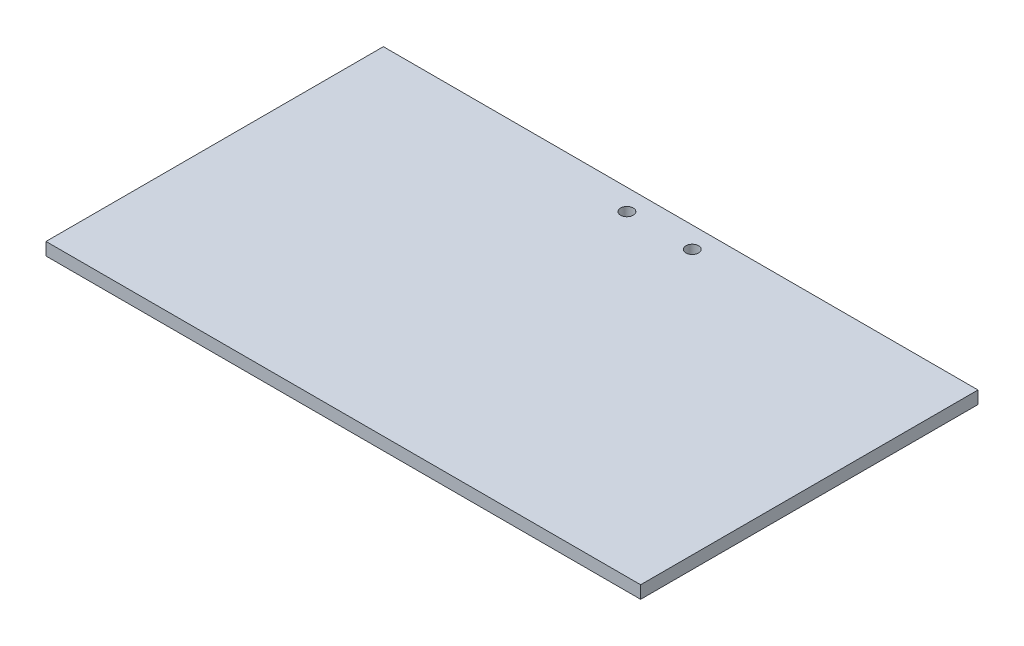
SolidWorks part; units mm, degrees
material "ｱｸﾘﾙ (中-上級の耐衝撃性)"
ref_plane "正面" through (0, 0, 0) normal (0, 0, 1) x (1, 0, 0)
ref_plane "平面" through (0, 0, 0) normal (0, 1, 0) x (1, 0, 0)
ref_plane "右側面" through (0, 0, 0) normal (1, 0, 0) x (0, 0, -1)
sketch "ｽｹｯﾁ1" plane through (0, 0, 0) normal (0, 1, 0) x (1, 0, 0)
  line L1 (0, 0) -> (-141, 0)
  line L2 (0, 0) -> (0, 80)
  line L3 (0, 80) -> (-141, 80)
  line L4 (-141, 0) -> (-141, 80)
  dimension "D1" = 141
  dimension "D2" = 80
extrude "ﾎﾞｽ - 押し出し1" add sketch "ｽｹｯﾁ1" along normal blind 3
sketch "ｽｹｯﾁ2" plane through (0, 3, 0) normal (0, 1, 0) x (1, 0, 0)
  line L0 (0, 80) -> (-141, 80) construction
  line L1 (-141, 80) -> (-141, 0) construction
  circle A0 centre (-78.25, 75) radius 1.5
  dimension "D1" = 3
  dimension "D2" = 5
  dimension "D3" = 62.75
extrude "ｶｯﾄ - 押し出し1" cut sketch "ｽｹｯﾁ2" against normal through all
sketch "ｽｹｯﾁ3" plane through (0, 3, 0) normal (0, 1, 0) x (1, 0, 0)
  line L0 (0, 80) -> (-141, 80) construction
  line L1 (0, 0) -> (0, 80) construction
  circle A0 centre (-62.75, 75) radius 1.5
  dimension "D1" = 3
  dimension "D2" = 5
  dimension "D3" = 62.75
extrude "ｶｯﾄ - 押し出し2" cut sketch "ｽｹｯﾁ3" against normal through all
